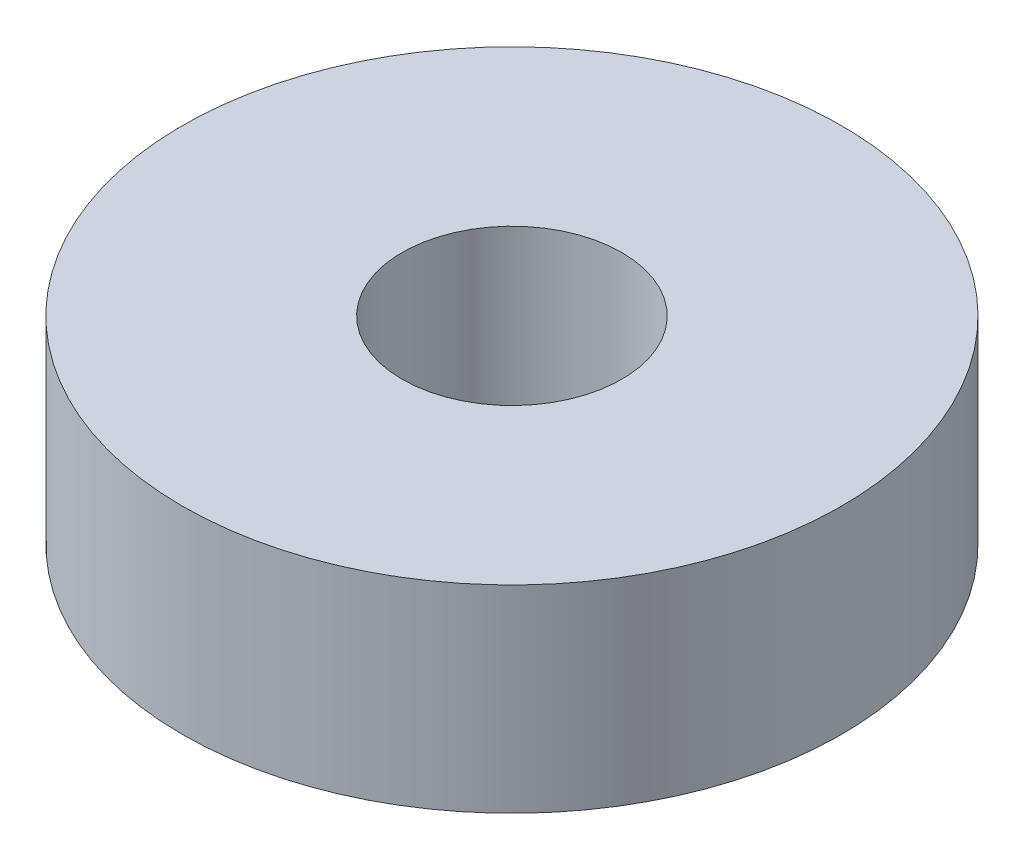
SolidWorks part; units mm, degrees
ref_plane "Front Plane" through (0, 0, 0) normal (0, 0, 1) x (1, 0, 0)
ref_plane "Top Plane" through (0, 0, 0) normal (0, 1, 0) x (1, 0, 0)
ref_plane "Right Plane" through (0, 0, 0) normal (1, 0, 0) x (0, 0, -1)
sketch "Sketch1" plane through (0, 0, 0) normal (0, 1, 0) x (1, 0, 0)
  circle A0 centre (0, 0) radius 3
  circle A1 centre (0, 0) radius 9
  dimension "D1" = 6
  dimension "D2" = 18
extrude "Boss-Extrude1" add sketch "Sketch1" along normal blind 5.4
